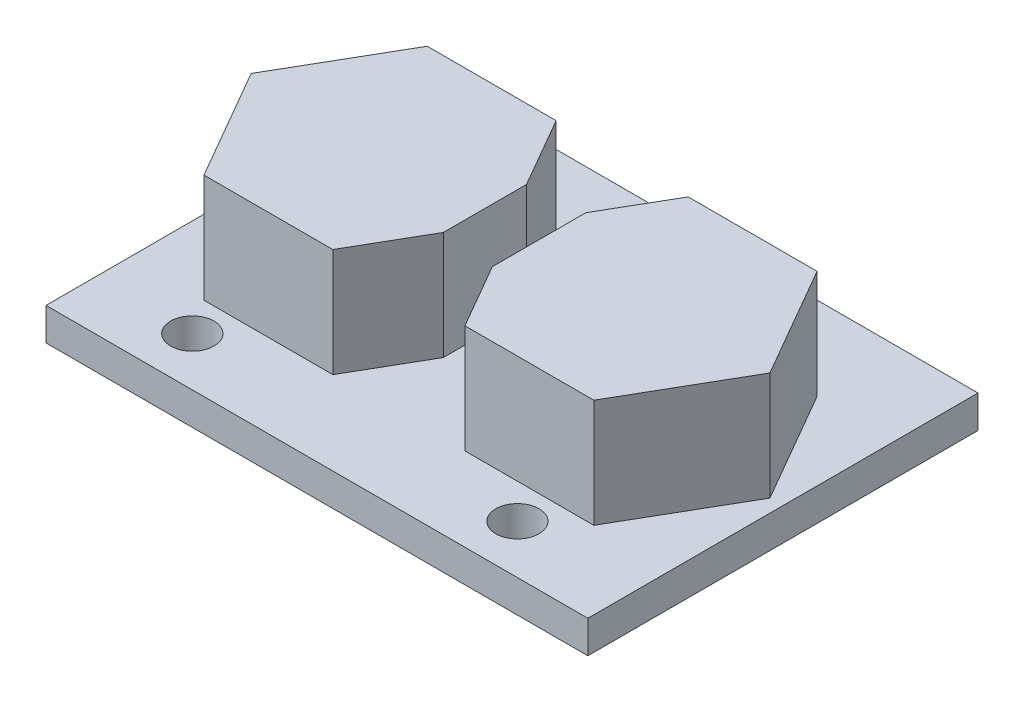
SolidWorks part; units mm, degrees
ref_plane "Front Plane" through (0, 0, 0) normal (0, 0, 1) x (1, 0, 0)
ref_plane "Top Plane" through (0, 0, 0) normal (0, 1, 0) x (1, 0, 0)
ref_plane "Right Plane" through (0, 0, 0) normal (1, 0, 0) x (0, 0, -1)
sketch "Sketch2" plane through (0, 0, 0) normal (0, 1, 0) x (1, 0, 0)
  line L1 (0, 0) -> (25, 0)
  line L2 (0, 0) -> (0, 18)
  line L3 (0, 18) -> (25, 18)
  line L4 (25, 0) -> (25, 18)
  dimension "D1" = 25
  dimension "D2" = 18
extrude "Boss-Extrude1" add sketch "Sketch2" along normal blind 1.5
sketch "Sketch3" plane through (0, 1.5, 0) normal (0, 1, 0) x (1, 0, 0)
  line L0 (0, 9) -> (25, 9) construction
  line L1 (0, 18) -> (0, 0) construction
  line L2 (25, 0) -> (25, 18) construction
  line L3 (25, 18) -> (0, 18) construction
  line L4 (9.3851, 3.85) -> (12.3584, 9)
  line L5 (12.3584, 9) -> (9.3851, 14.15)
  line L6 (9.3851, 14.15) -> (3.4384, 14.15)
  line L7 (3.4384, 14.15) -> (0.465, 9)
  line L8 (0.465, 9) -> (3.4384, 3.85)
  line L9 (3.4384, 3.85) -> (9.3851, 3.85)
  line L10 (12.4317, 18) -> (12.4317, 0) construction
  line L11 (0, 0) -> (25, 0) construction
  line L12 (21.4251, 3.85) -> (15.4784, 3.85)
  line L13 (24.3984, 9) -> (21.4251, 3.85)
  line L14 (21.4251, 14.15) -> (24.3984, 9)
  line L15 (15.4784, 14.15) -> (21.4251, 14.15)
  line L16 (12.505, 9) -> (15.4784, 14.15)
  line L17 (15.4784, 3.85) -> (12.505, 9)
  line L19 (13.75, 18) -> (11.25, 18)
  line L20 (13.75, 18) -> (13.75, 0)
  line L21 (13.75, 0) -> (11.25, 0)
  line L22 (11.25, 18) -> (11.25, 0)
  line L23 (13.75, 18) -> (11.25, 0) construction
  line L24 (13.75, 0) -> (11.25, 18) construction
  circle A0 centre (6.4117, 9) radius 5.15 construction
  circle A1 centre (18.4517, 9) radius 5.15 construction
  point P28 (12.5, 9)
  dimension "D1" = 10.3
  dimension "D2" = 0.465
  dimension "D3" = 2.5
  dimension "D4" = 12.04
extrude "Boss-Extrude2" add sketch "Sketch3" along normal blind 5 contours L22 L5 L6 L7 L8 L9 L4 | L16 L20 L17 L12 L13 L14 L15
sketch "Sketch5" plane through (0, 0, 0) normal (0, -1, 0) x (1, 0, 0)
  line L0 (0, -2.25) -> (25, -2.25) construction
  line L1 (0, -18) -> (0, 0) construction
  line L2 (25, 0) -> (25, -18) construction
  line L3 (2, 0) -> (2, -18) construction
  line L4 (0, 0) -> (25, 0) construction
  line L5 (25, -18) -> (0, -18) construction
  circle A0 centre (4.5, -2.25) radius 1
  circle A1 centre (19.5, -2.25) radius 1
  dimension "D4" = 2
  dimension "D1" = 2
  dimension "D2" = 2.25
  dimension "D3" = 2.5
  dimension "D5" = 15
extrude "Cut-Extrude1" cut sketch "Sketch5" against normal up to surface (1.5 mm away) up to face at (17.9579, 1.5, -9)
